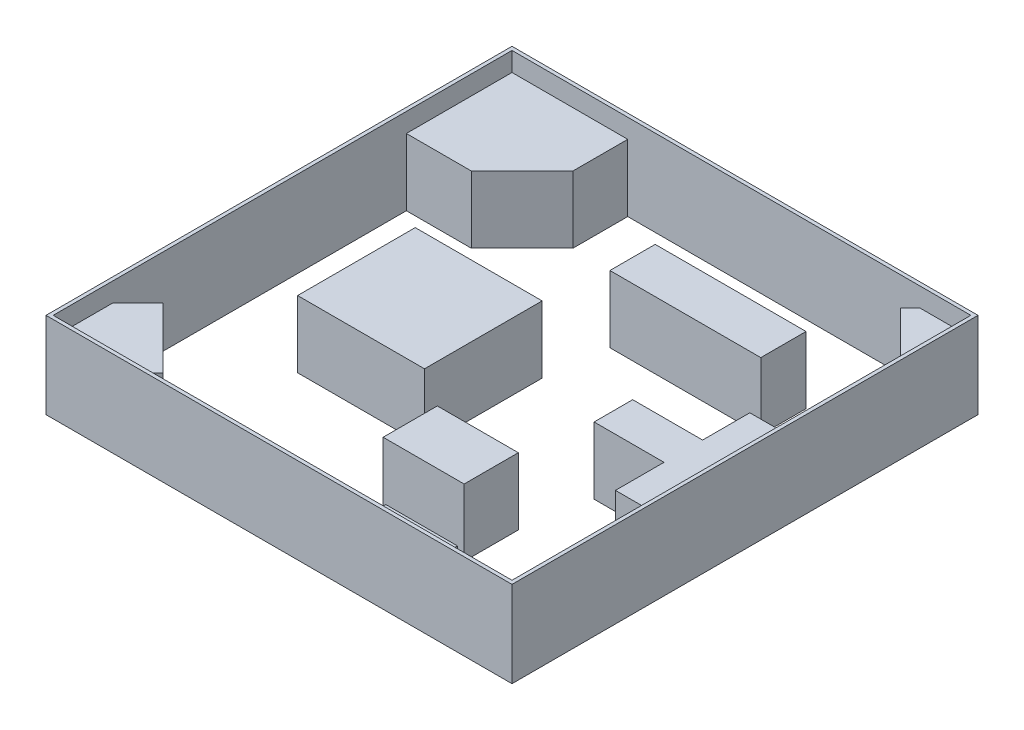
SolidWorks part; units mm, degrees
material "Maple"
ref_plane "Front Plane" through (0, 0, 0) normal (0, 0, 1) x (1, 0, 0)
ref_plane "Top Plane" through (0, 0, 0) normal (0, 1, 0) x (1, 0, 0)
ref_plane "Right Plane" through (0, 0, 0) normal (1, 0, 0) x (0, 0, -1)
sketch "Sketch1" plane through (0, 0, 0) normal (0, 1, 0) x (1, 0, 0)
  line L0 (-2476.5, 2476.5) -> (2476.5, 2476.5)
  line L1 (-2438.4, -2438.4) -> (2438.4, -2438.4)
  line L2 (-2438.4, -2438.4) -> (-2438.4, 2438.4)
  line L3 (-2438.4, 2438.4) -> (2438.4, 2438.4)
  line L4 (2438.4, -2438.4) -> (2438.4, 2438.4)
  line L5 (-2438.4, -2438.4) -> (2438.4, 2438.4) construction
  line L6 (-2438.4, 2438.4) -> (2438.4, -2438.4) construction
  line L7 (2476.5, -2476.5) -> (2476.5, 2476.5)
  line L8 (-2476.5, -2476.5) -> (2476.5, -2476.5)
  line L9 (-2476.5, -2476.5) -> (-2476.5, 2476.5)
  point P0 (0, 0)
  dimension "D1" = 4876.8
  dimension "D2" = 4876.8
  dimension "D3" = 38.1
extrude "Boss-Extrude1" add sketch "Sketch1" along normal blind 914.4
sketch "Sketch3" plane through (0, 0, 0) normal (0, 1, 0) x (1, 0, 0)
  line L0 (-271.1216, -204.4549) -> (-137.7883, -204.4549) construction
  line L1 (-1208.1663, 2438.4) -> (-1208.1663, 1859.1008)
  line L2 (2438.4, 2438.4) -> (-2438.4, 2438.4) construction
  line L3 (-1208.1663, 1859.1008) -> (-1747.9142, 1315.7943)
  line L4 (-1747.9142, 1315.7943) -> (-2438.4, 1315.7943)
  line L5 (-2438.4, 2438.4) -> (-2438.4, -2438.4) construction
  line L6 (-2438.4, 1315.7943) -> (-2438.4, 2438.4)
  line L7 (-2438.4, 2438.4) -> (-1208.1663, 2438.4)
  line L8 (1900.0602, 2438.4) -> (1796.3909, 2334.7307)
  line L9 (1796.3909, 2334.7307) -> (2316.9733, 1814.1482)
  line L10 (2316.9733, 1814.1482) -> (2438.4, 1935.5749)
  line L11 (2438.4, -2438.4) -> (2438.4, 2438.4) construction
  line L12 (2438.4, 1935.5749) -> (2438.4, 2438.4)
  line L13 (2438.4, 2438.4) -> (1900.0602, 2438.4)
  line L14 (-95.6266, 1617.3659) -> (1508.0314, 1617.3659)
  line L15 (1508.0314, 1617.3659) -> (1508.0314, 1136.2685)
  line L16 (1508.0314, 1136.2685) -> (-95.6266, 1136.2685)
  line L17 (-95.6266, 1136.2685) -> (-95.6266, 1617.3659)
  line L18 (-1524.9667, 496.4854) -> (-176.079, 496.4854)
  line L19 (-176.079, 496.4854) -> (-176.079, -753.9856)
  line L20 (-176.079, -753.9856) -> (-1524.9667, -753.9856)
  line L21 (-1524.9667, -753.9856) -> (-1524.9667, 496.4854)
  line L22 (234.038, -1027.8391) -> (1094.9215, -1027.8391)
  line L23 (1094.9215, -1027.8391) -> (1094.9215, -1603.7004)
  line L24 (1094.9215, -1603.7004) -> (234.038, -1603.7004)
  line L25 (234.038, -1603.7004) -> (234.038, -1027.8391)
  line L26 (2438.4, 569.9399) -> (1957.6596, 569.9399)
  line L27 (1957.6596, 569.9399) -> (1957.6596, 68.1742)
  line L28 (1957.6596, 68.1742) -> (1214.6603, 68.1742)
  line L29 (1214.6603, 68.1742) -> (1214.6603, -341.9228)
  line L30 (1214.6603, -341.9228) -> (1957.6596, -341.9228)
  line L31 (1957.6596, -341.9228) -> (1957.6596, -858.1626)
  line L32 (1957.6596, -858.1626) -> (2438.4, -858.1626)
  line L33 (2438.4, -858.1626) -> (2438.4, 569.9399)
  line L34 (1629.582, -2438.4) -> (1629.582, -2209.0703)
  line L35 (-2438.4, -2438.4) -> (2438.4, -2438.4) construction
  line L36 (1629.582, -2209.0703) -> (867.2841, -2209.0703)
  line L37 (867.2841, -2209.0703) -> (867.2841, -2438.4)
  line L38 (867.2841, -2438.4) -> (1629.582, -2438.4)
  line L39 (-1781.4601, -2438.4) -> (-1524.9667, -2181.9066)
  line L40 (-1524.9667, -2181.9066) -> (-2170.3453, -1536.528)
  line L41 (-2170.3453, -1536.528) -> (-2438.4, -1804.5827)
  line L42 (-2438.4, -1804.5827) -> (-2438.4, -2438.4)
  line L43 (-2438.4, -2438.4) -> (-1781.4601, -2438.4)
extrude "Boss-Extrude2" add sketch "Sketch3" along normal blind 711.2
